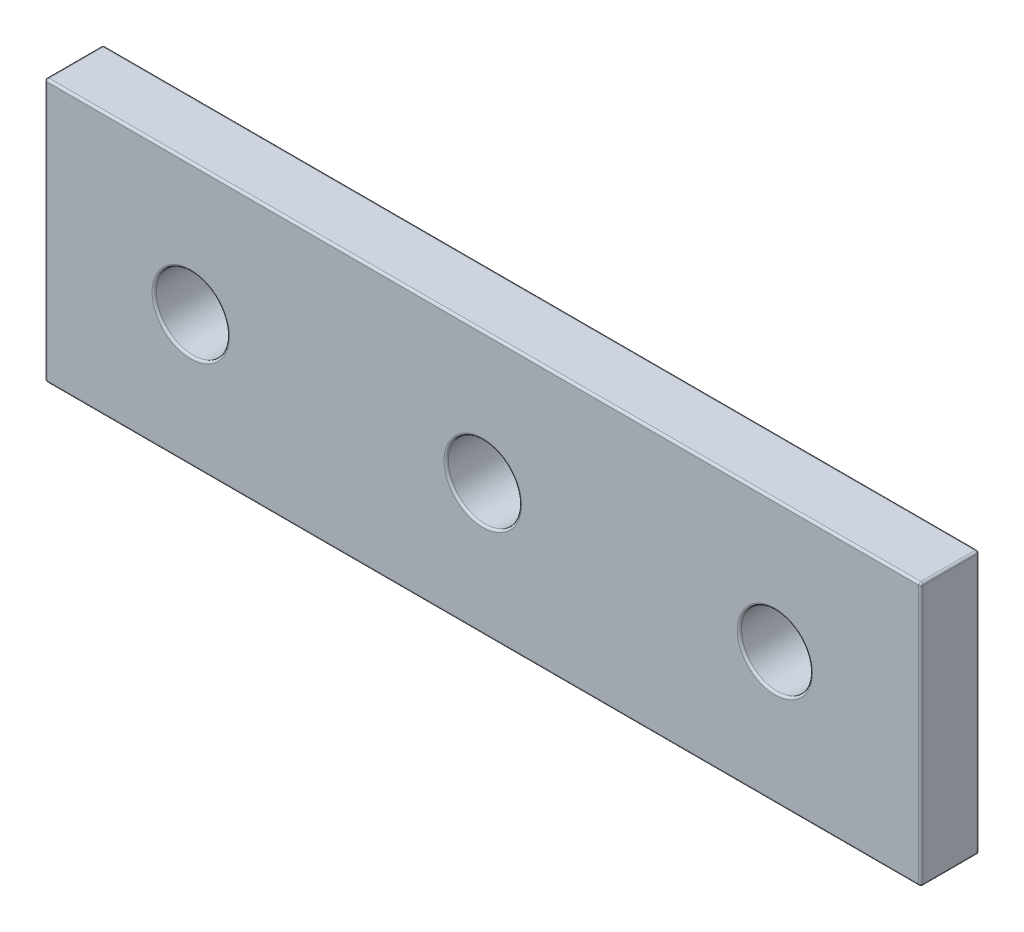
SolidWorks part; units mm, degrees
ref_plane "Front Plane" through (0, 0, 0) normal (0, 0, 1) x (1, 0, 0)
ref_plane "Top Plane" through (0, 0, 0) normal (0, 1, 0) x (1, 0, 0)
ref_plane "Right Plane" through (0, 0, 0) normal (1, 0, 0) x (0, 0, -1)
sketch "Sketch1" plane through (0, 0, 0) normal (0, 0, 1) x (1, 0, 0)
  line L0 (-30, -9) -> (30, 9) construction
  line L1 (-30, 9) -> (30, 9)
  line L2 (-30, 9) -> (-30, -9)
  line L3 (-30, -9) -> (30, -9)
  line L4 (30, 9) -> (30, -9)
  line L5 (-30, 9) -> (30, -9) construction
  line L6 (30, -9) -> (30, -8.177) construction
  circle A0 centre (0, 0) radius 2.5
  circle A1 centre (20, 0) radius 2.4258
  circle A2 centre (-20, 0) radius 2.5
  point P5 (0, 0)
  dimension "D3" = 5
  dimension "D1" = 18
  dimension "D2" = 60
  dimension "D4" = 20
  dimension "D5" = 20
extrude "Boss-Extrude1" add sketch "Sketch1" along normal blind 4 contours A0 | L3 L4 L1 L2 | A2 | A1
fillet "Fillet1" radius 0.15 18 edges at (22.4258, 0, 0) (2.5, 0, 0) (0, -9, 0) (30, 0, 0) (0, 9, 0) (-30, 0, 0) (-17.5, 0, 0) (22.4258, 0, 4) (2.5, 0, 4) (0, 9, 4) (30, 0, 4) (0, -9, 4) (-30, 0, 4) (-17.5, 0, 4) (-30, 9, 2) (-30, -9, 2) (30, -9, 2) (30, 9, 2)
